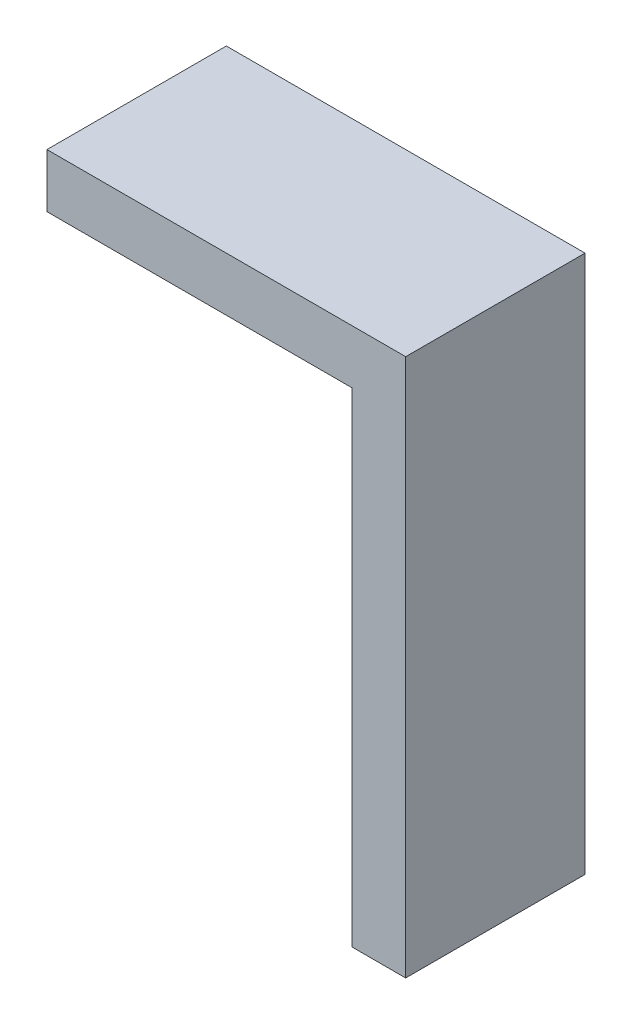
SolidWorks part; units mm, degrees
ref_plane "前视基准面" through (0, 0, 0) normal (0, 0, 1) x (1, 0, 0)
ref_plane "上视基准面" through (0, 0, 0) normal (0, 1, 0) x (1, 0, 0)
ref_plane "右视基准面" through (0, 0, 0) normal (1, 0, 0) x (0, 0, -1)
sketch "草图1" plane through (0, 0, 0) normal (0, 0, 1) x (1, 0, 0)
  line L8 (-47.828, 20.529) -> (-27.828, 20.529)
  line L9 (-27.828, 20.529) -> (-27.828, -9.471)
  line L10 (-27.828, -9.471) -> (-30.828, -9.471)
  line L11 (-30.828, -9.471) -> (-30.828, 17.529)
  line L12 (-30.828, 17.529) -> (-47.828, 17.529)
  line L13 (-47.828, 17.529) -> (-47.828, 20.529)
extrude "凸台-拉伸1" add sketch "草图1" along normal blind 10
